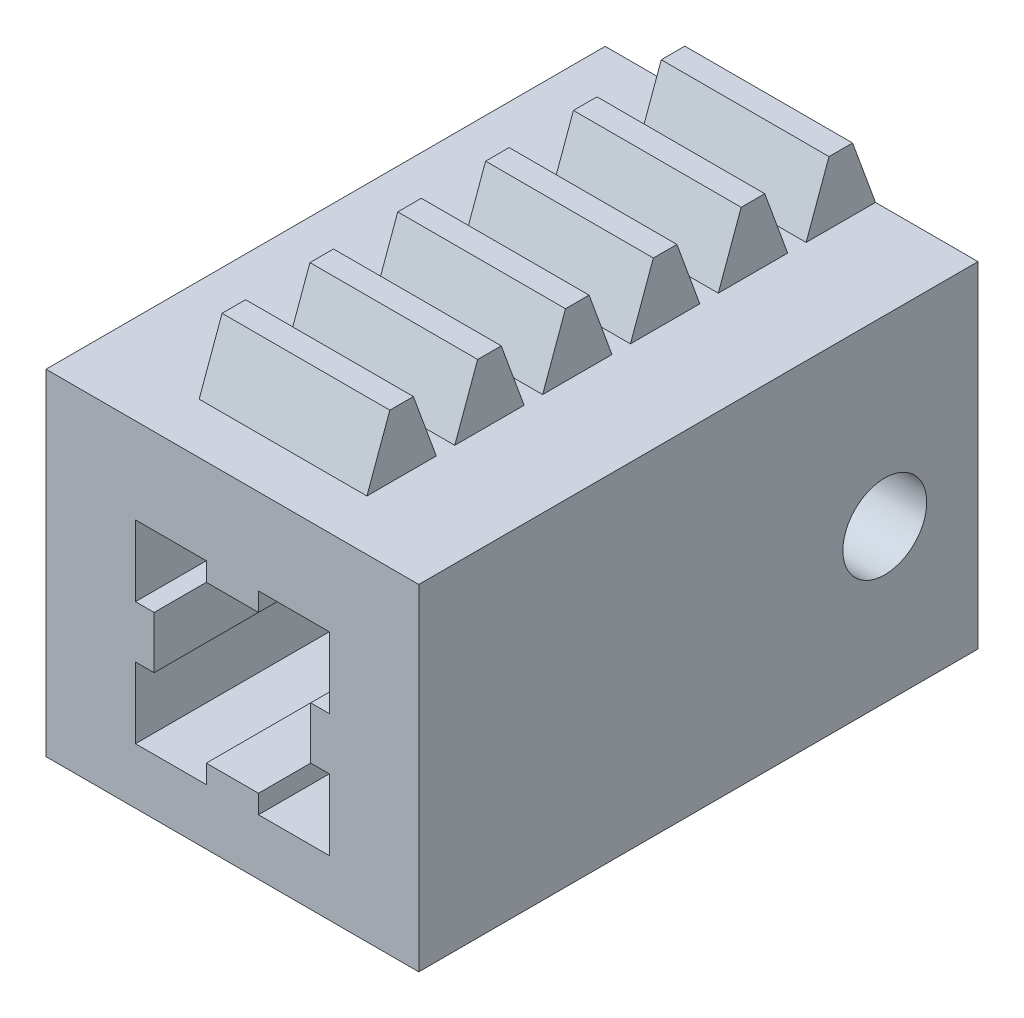
SolidWorks part; units mm, degrees
ref_plane "Front Plane" through (0, 0, 0) normal (0, 0, 1) x (1, 0, 0)
ref_plane "Top Plane" through (0, 0, 0) normal (0, 1, 0) x (1, 0, 0)
ref_plane "Right Plane" through (0, 0, 0) normal (1, 0, 0) x (0, 0, -1)
sketch "Esquisse1" plane through (0, 0, 0) normal (0, 0, 1) x (1, 0, 0)
  line L1 (-10, 9) -> (10, 9)
  line L2 (-10, 9) -> (-10, -9)
  line L3 (-10, -9) -> (10, -9)
  line L4 (10, 9) -> (10, -9)
  point P4 (0, -9)
  point P5 (-10, 0)
  dimension "D1" = 20
  dimension "D2" = 18
extrude "Main Extrusion" add sketch "Esquisse1" along normal blind 30
sketch "Esquisse3" plane through (0, 0, 0) normal (0, 0, -1) x (-1, 0, 0)
  line L0 (-5.2, 4.4) -> (-5.2, 0.6)
  line L1 (-5.2, 0.6) -> (-4.2, 0.6)
  line L2 (-4.2, 0.6) -> (-4.2, -2.2)
  line L3 (-4.2, -2.2) -> (-5.2, -2.2)
  line L4 (-5.2, -2.2) -> (-5.2, -6)
  line L5 (-5.2, -6) -> (-1.4, -6)
  line L6 (-1.4, -6) -> (-1.4, -5)
  line L7 (-1.4, -5) -> (1.4, -5)
  line L8 (1.4, -5) -> (1.4, -6)
  line L9 (1.4, -6) -> (5.2, -6)
  line L10 (5.2, -6) -> (5.2, -2.2)
  line L11 (5.2, -2.2) -> (4.2, -2.2)
  line L12 (4.2, -2.2) -> (4.2, 0.6)
  line L13 (4.2, 0.6) -> (5.2, 0.6)
  line L14 (5.2, 0.6) -> (5.2, 4.4)
  line L15 (5.2, 4.4) -> (1.4, 4.4)
  line L16 (1.4, 4.4) -> (1.4, 3.4)
  line L17 (1.4, 3.4) -> (-1.4, 3.4)
  line L18 (-1.4, 3.4) -> (-1.4, 4.4)
  line L19 (-1.4, 4.4) -> (-5.2, 4.4)
  line L21 (10, -9) -> (-10, -9) construction
  point P20 (0, -5)
  point P24 (0, -9)
  dimension "D1" = 2.8
  dimension "D2" = 10.4
  dimension "D3" = 1
  dimension "D4" = 1
  dimension "D5" = 3
extrude "Main Riding Hole" cut sketch "Esquisse3" against normal through all
sketch "Esquisse4" plane through (-10, 0, 0) normal (-1, 0, 0) x (0, 0, 1)
  line L1 (0, -2.2) -> (0, 0.6) construction
  line L2 (0, 9) -> (0, -9) construction
  circle A0 centre (5, -0.8) radius 2.25
  point P5 (0, -0.8)
  dimension "D1" = 4.5
  dimension "D2" = 5
extrude "TractorHole" cut sketch "Esquisse4" against normal blind 8
mirror "TractorHoleSymetry" about plane through (0, 0, 0) normal (1, 0, 0) of "TractorHole"
sketch "Esquisse8" plane through (0, 0, 0) normal (1, 0, 0) x (0, 0, -1)
  line L0 (-3.7211, 9) -> (-2.4927, 12.375)
  line L1 (-2.4927, 12.375) -> (-1.2284, 12.375)
  line L2 (-1.2284, 12.375) -> (0, 9)
  line L3 (-3.7211, 9) -> (-4.7124, 9) construction
  line L4 (-3.7211, 9) -> (0, 9)
  line L5 (-3.5846, 9.375) -> (-4.8489, 9.375) construction
  line L6 (-3.7211, 9) -> (-3.7211, 1.1813) construction
  line L7 (-4.7124, 9) -> (-5.3948, 10.875) construction
  line L8 (-5.3948, 10.875) -> (-0.6824, 10.875) construction
  point P6 (3.7211, 15.3667)
  point P11 (2.4927, 18.6899)
  point P12 (0, 12)
  point P13 (0, 9)
  point P14 (0, 0)
  point P15 (-1.6571, 17.875)
  point P16 (0, 14.5)
  dimension "D1" = 20
  dimension "D2" = 1.5
  dimension "D3" = 3.375
  dimension "D4" = 4.7124
  dimension "D5" = 3
extrude "Boss.-Extru.1" add sketch "Esquisse8" along normal mid plane 9
pattern_linear "Répétition linéaire1" count 6 spacing 4.7124 along (0, 0, 1) of "Boss.-Extru.1"
